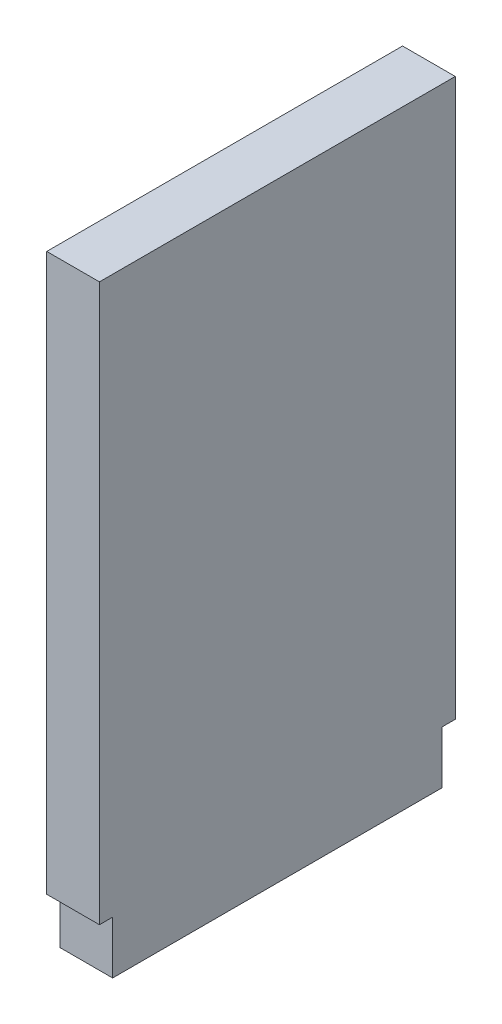
SolidWorks part; units mm, degrees
ref_plane "정면" through (0, 0, 0) normal (0, 0, 1) x (1, 0, 0)
ref_plane "윗면" through (0, 0, 0) normal (0, 1, 0) x (1, 0, 0)
ref_plane "우측면" through (0, 0, 0) normal (1, 0, 0) x (0, 0, -1)
sketch "스케치1" plane through (0, 0, 0) normal (1, 0, 0) x (0, 0, -1)
  line L0 (-9.5123, 0) -> (14.4726, 0) construction
  line L1 (-7.05, 1.3) -> (-7.05, 0.5)
  line L2 (-24.2092, 1.3) -> (25.0232, 1.3)
  line L3 (-24.2092, 1.3) -> (-24.2092, 0.5)
  line L4 (-24.2092, 0.5) -> (25.0232, 0.5)
  line L5 (25.0232, 1.3) -> (25.0232, 0.5)
  line L10 (7.05, 1.3) -> (7.05, 0.5)
  line L11 (11.65, 1.3) -> (11.65, 0.5)
  line L12 (-11.65, 1.3) -> (-11.65, 0.5)
  circle A0 centre (-7.05, 6.25) radius 6.25
  circle A1 centre (7.05, 6.25) radius 6.25
  circle A2 centre (0, 4.3) radius 1.8
  circle A3 centre (0, 4.3) radius 3
  circle A4 centre (-7.05, 6.25) radius 5.4
  circle A5 centre (7.05, 6.25) radius 5.4
  circle A6 centre (19.8088, 3.7) radius 2.4
  circle A7 centre (19.8088, 3.7) radius 2.95
  circle A8 centre (-7.05, 6.25) radius 3
  circle A9 centre (7.05, 6.25) radius 3
  point P23 (21.5242, 1.3)
  point P24 (18.0934, 1.3)
  dimension "D1" = 12.5
  dimension "D2" = 3.6
  dimension "D3" = 6
  dimension "D4" = 10.8
  dimension "D11" = 5.9
  dimension "D12" = 4.8
  dimension "D14" = 6
  dimension "D15" = 6
  dimension "D5" = 14.1
  dimension "D6" = 7.05
  dimension "D7" = 0.8
  dimension "D8" = 4.6
  dimension "D9" = 4.6
  dimension "D13" = 1
sketch "스케치2" plane through (0, 0, 0) normal (1, 0, 0) x (0, 0, -1)
  line L0 (-13.45, 1.3) -> (-11.65, 1.3)
  line L1 (-24.2092, 1.3) -> (25.0232, 1.3) construction
  line L2 (-11.65, 1.3) -> (-11.65, 0.5)
  line L3 (-11.65, 0.5) -> (-7.05, 0.5)
  line L4 (-7.05, 0.5) -> (-7.05, 1.3)
  line L5 (-7.05, 1.3) -> (-2, 1.3)
  line L6 (0, 6.49) -> (0, -6.49) construction
  line L7 (-13.45, 1.3) -> (-13.45, 12.3)
  line L8 (-13.45, 12.3) -> (-11.45, 12.3)
  line L9 (-11.45, 12.3) -> (-11.45, 10.3)
  line L10 (-2, 1.3) -> (-2, 2.0639)
  line L11 (-11.45, 10.3) -> (13.45, 10.3)
  line L12 (13.45, 10.3) -> (13.45, 1.3)
  line L13 (13.45, 1.3) -> (11.65, 1.3)
  line L14 (11.65, 1.3) -> (11.65, 0.5)
  line L15 (11.65, 0.5) -> (7.05, 0.5)
  line L16 (7.05, 0.5) -> (7.05, 1.3)
  line L17 (7.05, 1.3) -> (2, 1.3)
  line L18 (2, 1.3) -> (2, 2.0639)
  circle A0 centre (-7.05, 6.25) radius 3 construction
  circle A1 centre (-7.05, 6.25) radius 3
  circle A2 centre (7.05, 6.25) radius 3 construction
  circle A3 centre (7.05, 6.25) radius 3
  arc A8 (-2, 2.0639) -> (2, 2.0639) centre (0, 4.3) cw
  circle A9 centre (0, 4.3) radius 3 construction
  dimension "D1" = 1.8
  dimension "D2" = 2
  dimension "D3" = 2
  dimension "D4" = 6
  dimension "D7" = 2
sketch "스케치3" plane through (0, 0, 0) normal (1, 0, 0) x (0, 0, -1)
  line L0 (-2.5, 0) -> (2.5, 0)
  line L1 (-200009.5123, 0) -> (200014.4726, 0) construction
  line L3 (-2.5, 0) -> (-2.5, 0.8)
  line L4 (-2.5, 0.8) -> (-2.7, 0.8)
  line L5 (-2.7, 0.8) -> (-2.7, 9.25)
  line L6 (-2.7, 9.25) -> (2.7, 9.25)
  line L8 (0, 5.0875) -> (0, -5.0875) construction
  line L10 (2.5, 0.8) -> (2.7, 0.8)
  line L11 (2.5, 0) -> (2.5, 0.8)
  line L12 (2.7, 0.8) -> (2.7, 9.25)
  dimension "D3" = 8.45
  dimension "D4" = 0.8
extrude "보스-돌출1" add sketch "스케치3" along normal blind 0.8
